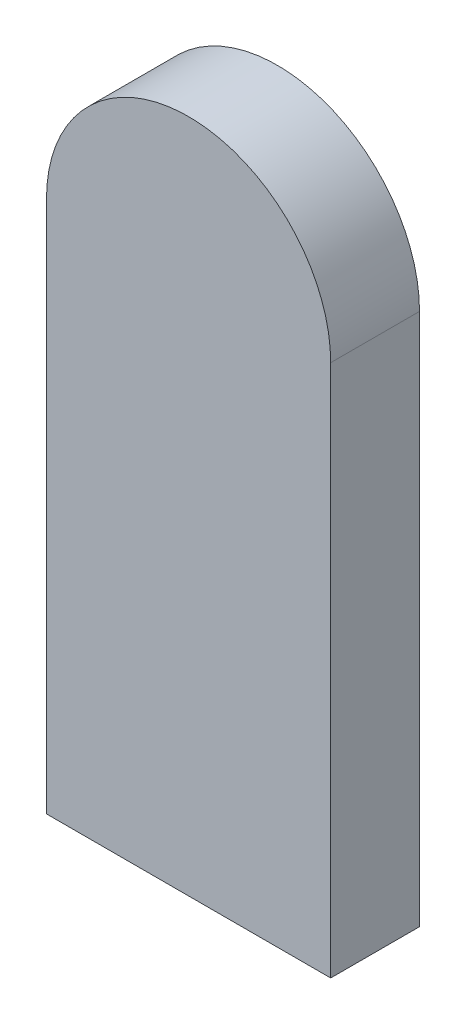
SolidWorks part; units mm, degrees
ref_plane "Piano frontale" through (0, 0, 0) normal (0, 0, 1) x (1, 0, 0)
ref_plane "Piano superiore" through (0, 0, 0) normal (0, 1, 0) x (1, 0, 0)
ref_plane "Piano destro" through (0, 0, 0) normal (1, 0, 0) x (0, 0, -1)
sketch "Schizzo1" plane through (0, 0, 0) normal (0, 0, 1) x (1, 0, 0)
  line L1 (-40, 0) -> (-40, -150)
  line L2 (40, 0) -> (40, -150)
  line L3 (-40, -150) -> (40, -150)
  arc A0 (40, 0) -> (-40, 0) centre (0, 0) ccw
  dimension "D1" = 80
  dimension "D2" = 150
extrude "Estrusione-Estrusione1" add sketch "Schizzo1" along normal blind 25
